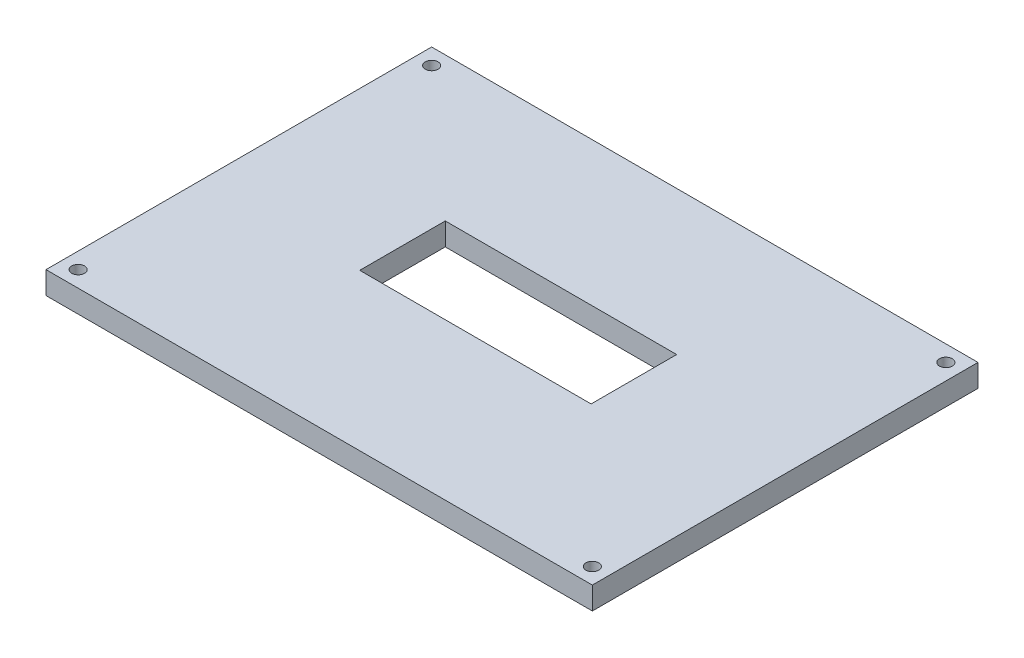
SolidWorks part; units mm, degrees
ref_plane "Front Plane" through (0, 0, 0) normal (0, 0, 1) x (1, 0, 0)
ref_plane "Top Plane" through (0, 0, 0) normal (0, 1, 0) x (1, 0, 0)
ref_plane "Right Plane" through (0, 0, 0) normal (1, 0, 0) x (0, 0, -1)
sketch "Sketch1" plane through (0, 0, 0) normal (0, 1, 0) x (1, 0, 0)
  line L1 (85, -60) -> (-85, -60)
  line L2 (85, -60) -> (85, 60)
  line L3 (85, 60) -> (-85, 60)
  line L4 (-85, -60) -> (-85, 60)
  line L5 (85, -60) -> (-85, 60) construction
  line L6 (85, 60) -> (-85, -60) construction
  point P0 (0, 0)
  dimension "D1" = 170
  dimension "D2" = 120
extrude "Boss-Extrude1" add sketch "Sketch1" along normal blind 7
sketch "Sketch2" plane through (0, 7, 0) normal (0, 1, 0) x (1, 0, 0)
  line L1 (-36, 15.2368) -> (36, 15.2368)
  line L2 (-36, 15.2368) -> (-36, -11.3838)
  line L3 (-36, -11.3838) -> (36, -11.3838)
  line L4 (36, 15.2368) -> (36, -11.3838)
  line L5 (-36, 15.2368) -> (36, -11.3838) construction
  line L6 (-36, -11.3838) -> (36, 15.2368) construction
  point P0 (0, 1.9265)
  point P5 (-15.2368, 7.706)
  point P6 (0, 1.9265)
  point P7 (0, 0)
  dimension "D1" = 72
  dimension "D2" = 26.6206
extrude "Cut-Extrude1" cut sketch "Sketch2" against normal blind 7
sketch "Sketch3" plane through (0, 7, 0) normal (0, 1, 0) x (1, 0, 0)
  line L1 (85, 60) -> (-85, 60) construction
  line L2 (-85, 60) -> (-85, -60) construction
  circle A0 centre (-80, 55) radius 2
  circle A1 centre (-70, -45.36) radius 2
  point P2 (0, 0)
  point P3 (0, 0)
  point P7 (-107.5802, 46.6895)
  dimension "D1" = 5
  dimension "D3" = 4
  dimension "D4" = 4
  dimension "D2" = 120
  dimension "D5" = 5
sketch "Sketch6" plane through (0, 7, 0) normal (0, 1, 0) x (1, 0, 0)
  line L0 (85, -60) -> (85, 60) construction
  line L1 (-85, -60) -> (85, -60) construction
  line L2 (85, 60) -> (-85, 60) construction
  circle A0 centre (80, -55) radius 2
  circle A1 centre (80, 55) radius 2
  point P4 (0, 0)
  point P5 (0, 0)
  point P6 (0, 0)
  point P7 (0, 0)
  point P8 (0, 0)
  dimension "D1" = 5
  dimension "D2" = 5
  dimension "D3" = 5
  dimension "D4" = 5
extrude "Cut-Extrude5" cut sketch "Sketch3" against normal blind 7 contours A0
sketch "Sketch7" plane through (0, 7, 0) normal (0, 1, 0) x (1, 0, 0)
  line L0 (-85, -60) -> (85, -60) construction
  line L1 (-85, 60) -> (-85, -60) construction
  circle A0 centre (-80, -55) radius 2
  dimension "D1" = 5
  dimension "D2" = 5
extrude "Cut-Extrude7" cut sketch "Sketch7" against normal blind 10
extrude "Cut-Extrude10" cut sketch "Sketch6" against normal blind 10 contours A1
sketch "Sketch9" plane through (0, 7, 0) normal (0, 1, 0) x (1, 0, 0)
  line L0 (85, -60) -> (85, 60) construction
  line L1 (-85, -60) -> (85, -60) construction
  circle A0 centre (80, -55) radius 2
  dimension "D1" = 5
  dimension "D2" = 5
extrude "Cut-Extrude11" cut sketch "Sketch9" against normal blind 10
